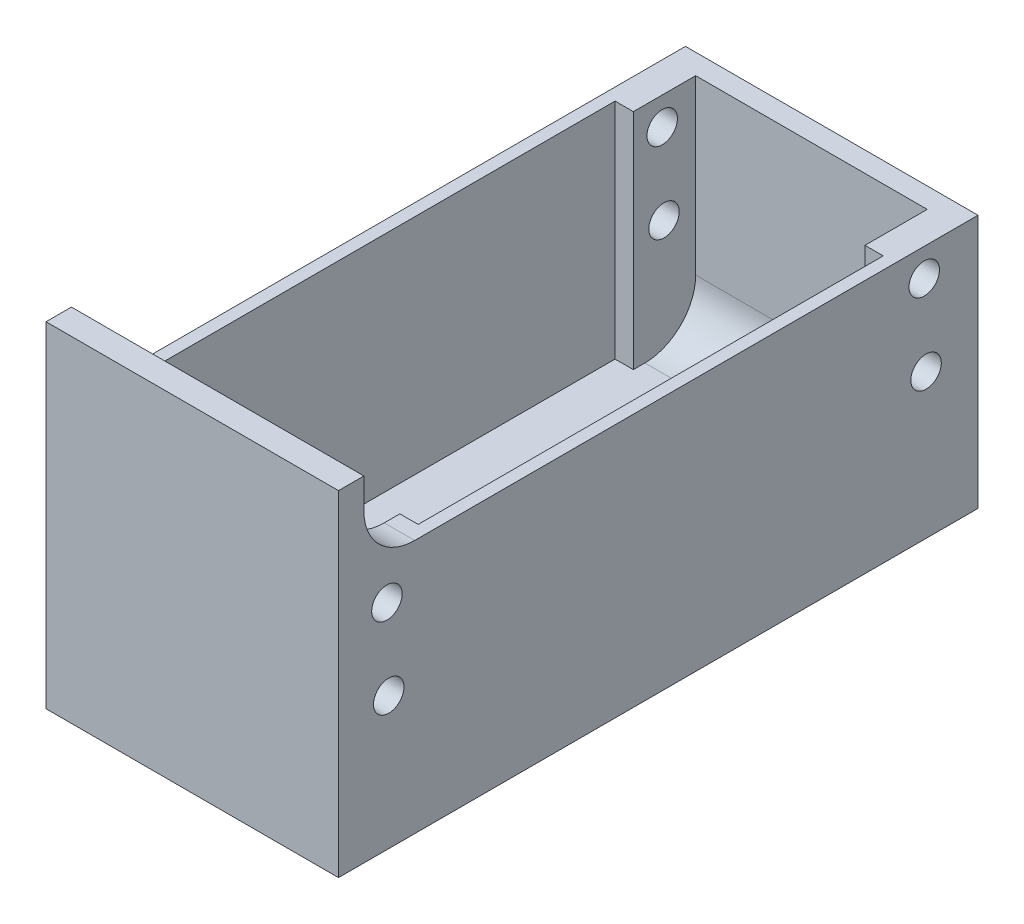
SolidWorks part; units mm, degrees
ref_plane "前视基准面" through (0, 0, 0) normal (0, 0, 1) x (1, 0, 0)
ref_plane "上视基准面" through (0, 0, 0) normal (0, 1, 0) x (1, 0, 0)
ref_plane "右视基准面" through (0, 0, 0) normal (1, 0, 0) x (0, 0, -1)
sketch "草图1" plane through (0, 0, 0) normal (0, 0, 1) x (1, 0, 0)
  line L0 (-13.7502, 26.8931) -> (-13.7502, 1.8931)
  line L1 (-13.7502, 1.8931) -> (15.0498, 1.8931)
  line L2 (15.0498, 1.8931) -> (15.0498, 26.8931)
  line L3 (15.0498, 26.8931) -> (12.0498, 26.8931)
  line L4 (12.0498, 26.8931) -> (12.0498, 4.8931)
  line L5 (12.0498, 4.8931) -> (-10.7502, 4.8931)
  line L6 (-10.7502, 4.8931) -> (-10.7502, 26.8931)
  line L7 (-10.7502, 26.8931) -> (-13.7502, 26.8931)
  dimension "D1" = 28.8
  dimension "D2" = 3
  dimension "D3" = 3
  dimension "D4" = 25
  dimension "D7" = 3
extrude "凸台-拉伸1" add sketch "草图1" along normal blind 62.96
sketch "草图2" plane through (0, 4.8931, 0) normal (0, 1, 0) x (1, 0, 0)
  line L0 (-13.7502, -31.48) -> (3.4081, -31.48) construction
  line L1 (15.0498, -62.96) -> (15.0498, 0) construction
  line L2 (-13.7502, 0) -> (15.0498, 0)
  line L3 (-13.7502, 0) -> (-13.7502, -2)
  line L4 (-13.7502, -2) -> (15.0498, -2)
  line L5 (15.0498, 0) -> (15.0498, -2)
  line L6 (-13.7502, -62.96) -> (-13.7502, 0) construction
  dimension "D1" = 2
extrude "凸台-拉伸2" add sketch "草图2" along normal up to surface (22 mm away) up to face at (13.5498, 26.8931, 31.48)
sketch "草图7" plane through (0, 4.8931, 0) normal (0, 1, 0) x (1, 0, 0)
  line L1 (-10.7502, -53.9223) -> (-12.5502, -53.9223)
  line L2 (-10.7502, -53.9223) -> (-10.7502, -8.1303)
  line L3 (-10.7502, -8.1303) -> (-12.5502, -8.1303)
  line L4 (-12.5502, -53.9223) -> (-12.5502, -8.1303)
  line L5 (12.0498, -53.9223) -> (13.8498, -53.9223)
  line L6 (12.0498, -53.9223) -> (12.0498, -8.1303)
  line L7 (12.0498, -8.1303) -> (13.8498, -8.1303)
  line L8 (13.8498, -53.9223) -> (13.8498, -8.1303)
  dimension "D1" = 1.8
  dimension "D2" = 1.8
extrude "切除-拉伸1" cut sketch "草图7" along normal up to surface (22 mm away) up to face at (0.6498, 26.8931, 31.98)
fillet "圆角2" radius 5 1 edges at (0.6498, 4.8931, 2)
hole_wizard "大小mm Press 暗销孔3" positions "草图12" profile "草图13" hole size "Ø3.0" standard "ISO" end condition through all
sketch "草图12" plane through (15.0498, 207.5446, -30.8813) normal (1, 0, 0) x (0, -0.0223, 0.9998)
  point P0 (93.1614, 190.5782)
  point P2 (93.1614, 182.5471)
  point P4 (40.2454, 190.5782)
  point P5 (40.2454, 182.5471)
sketch "草图13" plane through (15.0498, 14.9405, 58.016) normal (0, 1, 0) x (0, 0, -1)
  line L0 (0, 0) -> (0, 28.8)
  line L1 (0, 28.8) -> (1.5, 28.8)
  line L2 (1.5, 28.8) -> (1.5, 0)
  line L3 (1.5, 0) -> (0, 0)
  line L4 (0, -6.35) -> (0, 107.95) construction
  dimension "通孔孔直径" = 3
  dimension "通孔孔深度" = 28.8
sketch "草图14" plane through (0, 4.8931, 0) normal (0, 1, 0) x (1, 0, 0)
  line L0 (15.0498, -62.96) -> (15.0498, 0) construction
  line L1 (-13.7502, -62.96) -> (15.0498, -62.96)
  line L2 (-13.7502, -62.96) -> (-13.7502, -60.46)
  line L3 (-13.7502, -60.46) -> (15.0498, -60.46)
  line L4 (15.0498, -62.96) -> (15.0498, -60.46)
  dimension "D1" = 2.5
extrude "凸台-拉伸3" add sketch "草图14" along normal blind 30
fillet "圆角3" radius 6 1 edges at (0.6498, 4.8931, 60.46)
fillet "圆角4" radius 5 2 edges at (13.5498, 26.8931, 60.46) (-12.2502, 26.8931, 60.46)
